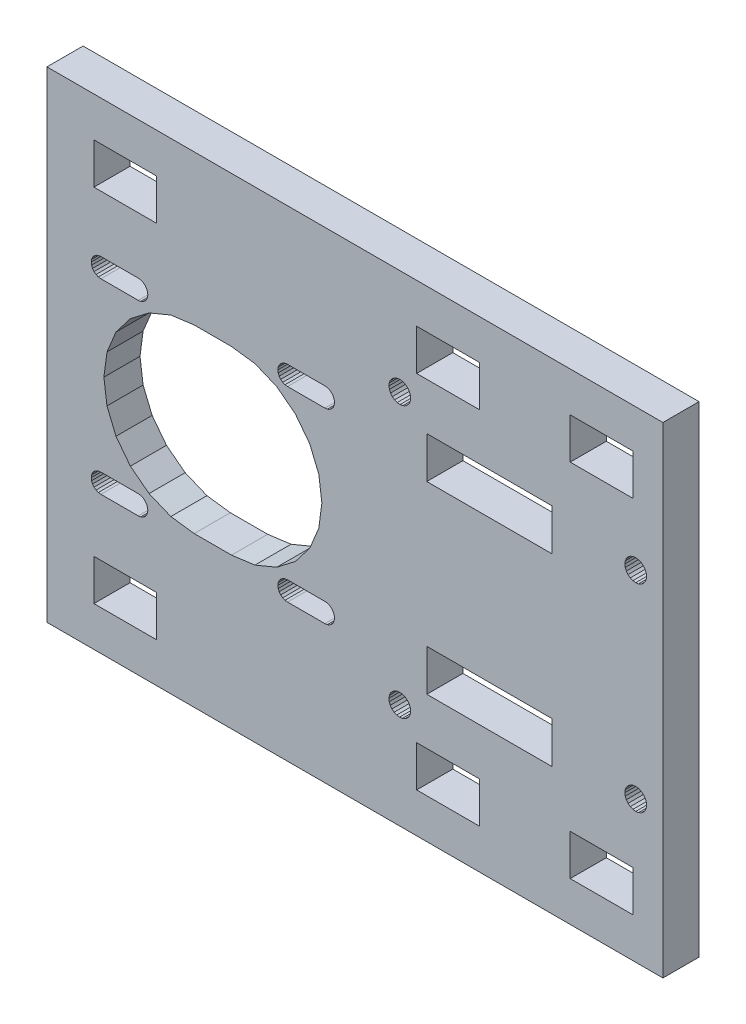
SolidWorks part; units mm, degrees
material "Maple"
ref_plane "Front Plane" through (0, 0, 0) normal (0, 0, 1) x (1, 0, 0)
ref_plane "Top Plane" through (0, 0, 0) normal (0, 1, 0) x (1, 0, 0)
ref_plane "Right Plane" through (0, 0, 0) normal (1, 0, 0) x (0, 0, -1)
sketch "Sketch1" plane through (0, 0, 0) normal (0, 0, 1) x (1, 0, 0)
  line L1749 (-500.5127, -309.2377) -> (-500.767, -309.5691)
  line L1750 (-500.767, -309.5691) -> (-500.9268, -309.955)
  line L1751 (-500.9268, -309.955) -> (-500.9814, -310.3691)
  line L1752 (-500.9814, -310.3691) -> (-500.9268, -310.7832)
  line L1753 (-500.9268, -310.7832) -> (-500.767, -311.1691)
  line L1754 (-491.6359, -309.955) -> (-491.7957, -309.5691)
  line L1755 (-491.7957, -309.5691) -> (-492.05, -309.2377)
  line L1756 (-492.05, -309.2377) -> (-492.3814, -308.9835)
  line L1757 (-492.3814, -308.9835) -> (-492.7672, -308.8236)
  line L1758 (-500.5376, -292.5691) -> (-500.5376, -299.3691)
  line L1759 (-500.5376, -299.3691) -> (-490.1376, -299.3691)
  line L1760 (-490.1376, -359.2691) -> (-490.1376, -352.4691)
  line L1761 (-490.1376, -352.4691) -> (-500.5376, -352.4691)
  line L1762 (-500.5376, -352.4691) -> (-500.5376, -359.2691)
  line L1763 (-491.6359, -310.7832) -> (-491.5814, -310.3691)
  line L1764 (-491.5814, -310.3691) -> (-491.6359, -309.955)
  line L1765 (-411.4551, -307.9103) -> (-411.021, -307.7304)
  line L1766 (-411.8279, -308.1963) -> (-411.4551, -307.9103)
  line L1767 (-406.0393, -285.9691) -> (-508.3376, -285.9691)
  line L1768 (-508.3376, -365.8691) -> (-406.0393, -365.8691)
  line L1769 (-446.9376, -299.3691) -> (-436.5376, -299.3691)
  line L1770 (-436.5376, -299.3691) -> (-436.5376, -292.5691)
  line L1771 (-421.4376, -359.2691) -> (-421.4376, -352.4691)
  line L1772 (-448.1592, -347.5539) -> (-447.9891, -347.9919)
  line L1773 (-448.4369, -347.1748) -> (-448.1592, -347.5539)
  line L1774 (-448.8033, -346.8806) -> (-448.4369, -347.1748)
  line L1775 (-469.5127, -340.2377) -> (-469.767, -340.5691)
  line L1776 (-473.7991, -311.3802) -> (-477.6814, -310.8691)
  line L1777 (-483.8814, -310.8691) -> (-477.6814, -310.8691)
  line L1778 (-483.8814, -310.8691) -> (-487.7636, -311.3802)
  line L1779 (-487.7636, -311.3802) -> (-491.3814, -312.8787)
  line L1780 (-448.8033, -304.9576) -> (-449.2333, -305.147)
  line L1781 (-448.4369, -304.6634) -> (-448.8033, -304.9576)
  line L1782 (-448.1592, -304.2843) -> (-448.4369, -304.6634)
  line L1783 (-462.6814, -325.8691) -> (-463.1925, -321.9868)
  line L1784 (-463.1925, -321.9868) -> (-464.691, -318.3691)
  line L1785 (-464.691, -318.3691) -> (-467.0747, -315.2625)
  line L1786 (-467.0747, -315.2625) -> (-470.1814, -312.8787)
  line L1787 (-492.7672, -311.9146) -> (-492.3814, -311.7547)
  line L1788 (-492.3814, -311.7547) -> (-492.05, -311.5005)
  line L1789 (-492.05, -311.5005) -> (-491.7957, -311.1691)
  line L1790 (-490.1376, -299.3691) -> (-490.1376, -292.5691)
  line L1791 (-490.1376, -292.5691) -> (-500.5376, -292.5691)
  line L1792 (-491.5814, -341.3691) -> (-491.6359, -340.955)
  line L1793 (-491.6359, -340.955) -> (-491.7957, -340.5691)
  line L1794 (-491.7957, -340.5691) -> (-492.05, -340.2377)
  line L1795 (-492.05, -340.2377) -> (-492.3814, -339.9835)
  line L1796 (-461.05, -340.2377) -> (-461.3814, -339.9835)
  line L1797 (-461.3814, -339.9835) -> (-461.7672, -339.8236)
  line L1798 (-406.0393, -365.8691) -> (-406.0393, -285.9691)
  line L1799 (-412.2937, -341.9032) -> (-412.1139, -341.4691)
  line L1800 (-449.3104, -350.1677) -> (-449.7775, -350.2187)
  line L1801 (-448.8724, -349.9975) -> (-449.3104, -350.1677)
  line L1802 (-448.4933, -349.7198) -> (-448.8724, -349.9975)
  line L1803 (-448.1991, -349.3534) -> (-448.4933, -349.7198)
  line L1804 (-498.8814, -325.8691) -> (-498.3702, -329.7514)
  line L1805 (-498.3702, -329.7514) -> (-496.8717, -333.3691)
  line L1806 (-496.8717, -333.3691) -> (-494.488, -336.4757)
  line L1807 (-494.488, -336.4757) -> (-491.3814, -338.8595)
  line L1808 (-409.2823, -310.7419) -> (-409.6551, -311.0279)
  line L1809 (-447.9891, -303.8463) -> (-448.1592, -304.2843)
  line L1810 (-450.6719, -349.9576) -> (-451.0383, -349.6634)
  line L1811 (-450.2419, -350.147) -> (-450.6719, -349.9576)
  line L1812 (-449.7775, -350.2187) -> (-450.2419, -350.147)
  line L1813 (-408.7551, -309.4691) -> (-408.8164, -309.935)
  line L1814 (-408.8164, -309.0032) -> (-408.7551, -309.4691)
  line L1815 (-408.9962, -308.5691) -> (-408.8164, -309.0032)
  line L1816 (-508.3376, -285.9691) -> (-508.3376, -365.8691)
  line L1817 (-411.4551, -340.8103) -> (-411.021, -340.6304)
  line L1818 (-448.0097, -348.9234) -> (-448.1991, -349.3534)
  line L1819 (-421.4376, -359.2691) -> (-411.0376, -359.2691)
  line L1820 (-411.0376, -359.2691) -> (-411.0376, -352.4691)
  line L1821 (-411.0376, -352.4691) -> (-421.4376, -352.4691)
  line L1822 (-469.1814, -311.7547) -> (-468.7955, -311.9146)
  line L1823 (-468.7955, -311.9146) -> (-468.3814, -311.9691)
  line L1824 (-468.3814, -311.9691) -> (-462.1814, -311.9691)
  line L1825 (-462.1814, -311.9691) -> (-461.7672, -311.9146)
  line L1826 (-461.7672, -311.9146) -> (-461.3814, -311.7547)
  line L1827 (-424.4866, -344.6691) -> (-445.2551, -344.6691)
  line L1828 (-424.4866, -344.6691) -> (-424.4866, -337.7691)
  line L1829 (-424.4866, -337.7691) -> (-445.2551, -337.7691)
  line L1830 (-469.1814, -342.7547) -> (-468.7955, -342.9146)
  line L1831 (-468.7955, -342.9146) -> (-468.3814, -342.9691)
  line L1832 (-468.3814, -342.9691) -> (-462.1814, -342.9691)
  line L1833 (-469.9268, -340.955) -> (-469.9814, -341.3691)
  line L1834 (-469.9814, -341.3691) -> (-469.9268, -341.7832)
  line L1835 (-469.9268, -341.7832) -> (-469.767, -342.1691)
  line L1836 (-469.767, -342.1691) -> (-469.5127, -342.5005)
  line L1837 (-500.1814, -339.9835) -> (-500.5127, -340.2377)
  line L1838 (-500.5127, -340.2377) -> (-500.767, -340.5691)
  line L1839 (-500.767, -340.5691) -> (-500.9268, -340.955)
  line L1840 (-500.9268, -340.955) -> (-500.9814, -341.3691)
  line L1841 (-445.2551, -337.7691) -> (-445.2551, -344.6691)
  line L1842 (-424.4866, -314.0691) -> (-445.2551, -314.0691)
  line L1843 (-424.4866, -314.0691) -> (-424.4866, -307.1691)
  line L1844 (-462.1814, -342.9691) -> (-461.7672, -342.9146)
  line L1845 (-461.7672, -342.9146) -> (-461.3814, -342.7547)
  line L1846 (-461.3814, -342.7547) -> (-461.05, -342.5005)
  line L1847 (-461.05, -342.5005) -> (-460.7957, -342.1691)
  line L1848 (-460.7957, -342.1691) -> (-460.6359, -341.7832)
  line L1849 (-412.1139, -341.4691) -> (-411.8279, -341.0963)
  line L1850 (-412.3551, -342.3691) -> (-412.2937, -341.9032)
  line L1851 (-412.2937, -342.835) -> (-412.3551, -342.3691)
  line L1852 (-408.9962, -341.4691) -> (-408.8164, -341.9032)
  line L1853 (-409.2823, -341.0963) -> (-408.9962, -341.4691)
  line L1854 (-409.6551, -340.8103) -> (-409.2823, -341.0963)
  line L1855 (-451.2761, -304.3534) -> (-451.4655, -303.9234)
  line L1856 (-450.9819, -304.7198) -> (-451.2761, -304.3534)
  line L1857 (-450.6029, -304.9975) -> (-450.9819, -304.7198)
  line L1858 (-450.6719, -301.8806) -> (-450.2419, -301.6912)
  line L1859 (-451.0383, -302.1748) -> (-450.6719, -301.8806)
  line L1860 (-451.316, -302.5539) -> (-451.0383, -302.1748)
  line L1861 (-448.4933, -302.1184) -> (-448.1991, -302.4848)
  line L1862 (-448.8724, -301.8407) -> (-448.4933, -302.1184)
  line L1863 (-421.4376, -299.3691) -> (-421.4376, -292.5691)
  line L1864 (-421.4376, -299.3691) -> (-411.0376, -299.3691)
  line L1865 (-412.1139, -343.2691) -> (-412.2937, -342.835)
  line L1866 (-411.8279, -343.6419) -> (-412.1139, -343.2691)
  line L1867 (-411.4551, -343.9279) -> (-411.8279, -343.6419)
  line L1868 (-461.7672, -339.8236) -> (-462.1814, -339.7691)
  line L1869 (-411.021, -311.2078) -> (-411.4551, -311.0279)
  line L1870 (-410.5551, -311.2691) -> (-411.021, -311.2078)
  line L1871 (-409.6551, -311.0279) -> (-410.0892, -311.2078)
  line L1872 (-449.2333, -346.6912) -> (-448.8033, -346.8806)
  line L1873 (-449.6977, -346.6195) -> (-449.2333, -346.6912)
  line L1874 (-450.1649, -346.6705) -> (-449.6977, -346.6195)
  line L1875 (-409.2823, -308.1963) -> (-408.9962, -308.5691)
  line L1876 (-409.6551, -307.9103) -> (-409.2823, -308.1963)
  line L1877 (-461.7672, -308.8236) -> (-462.1814, -308.7691)
  line L1878 (-468.3814, -308.7691) -> (-462.1814, -308.7691)
  line L1879 (-468.3814, -308.7691) -> (-468.7955, -308.8236)
  line L1880 (-468.7955, -308.8236) -> (-469.1814, -308.9835)
  line L1881 (-469.1814, -308.9835) -> (-469.5127, -309.2377)
  line L1882 (-469.5127, -309.2377) -> (-469.767, -309.5691)
  line L1883 (-469.767, -309.5691) -> (-469.9268, -309.955)
  line L1884 (-469.9268, -309.955) -> (-469.9814, -310.3691)
  line L1885 (-469.9814, -310.3691) -> (-469.9268, -310.7832)
  line L1886 (-408.9962, -310.3691) -> (-409.2823, -310.7419)
  line L1887 (-408.8164, -309.935) -> (-408.9962, -310.3691)
  line L1888 (-492.7672, -308.8236) -> (-493.1814, -308.7691)
  line L1889 (-499.3814, -308.7691) -> (-493.1814, -308.7691)
  line L1890 (-499.3814, -308.7691) -> (-499.7955, -308.8236)
  line L1891 (-499.7955, -308.8236) -> (-500.1814, -308.9835)
  line L1892 (-500.1814, -308.9835) -> (-500.5127, -309.2377)
  line L1893 (-411.021, -344.1078) -> (-411.4551, -343.9279)
  line L1894 (-410.5551, -344.1691) -> (-411.021, -344.1078)
  line L1895 (-409.6551, -343.9279) -> (-410.0892, -344.1078)
  line L1896 (-409.2823, -343.6419) -> (-409.6551, -343.9279)
  line L1897 (-469.9268, -310.7832) -> (-469.767, -311.1691)
  line L1898 (-469.767, -311.1691) -> (-469.5127, -311.5005)
  line L1899 (-469.5127, -311.5005) -> (-469.1814, -311.7547)
  line L1900 (-451.4862, -302.9919) -> (-451.316, -302.5539)
  line L1901 (-451.5372, -303.459) -> (-451.4862, -302.9919)
  line L1902 (-451.4655, -303.9234) -> (-451.5372, -303.459)
  line L1903 (-500.9814, -341.3691) -> (-500.9268, -341.7832)
  line L1904 (-500.9268, -341.7832) -> (-500.767, -342.1691)
  line L1905 (-500.767, -342.1691) -> (-500.5127, -342.5005)
  line L1906 (-500.5127, -342.5005) -> (-500.1814, -342.7547)
  line L1907 (-424.4866, -307.1691) -> (-445.2551, -307.1691)
  line L1908 (-445.2551, -307.1691) -> (-445.2551, -314.0691)
  line L1909 (-436.5376, -352.4691) -> (-446.9376, -352.4691)
  line L1910 (-446.9376, -352.4691) -> (-446.9376, -359.2691)
  line L1911 (-412.1139, -308.5691) -> (-411.8279, -308.1963)
  line L1912 (-412.2937, -309.0032) -> (-412.1139, -308.5691)
  line L1913 (-436.5376, -359.2691) -> (-436.5376, -352.4691)
  line L1914 (-436.5376, -292.5691) -> (-446.9376, -292.5691)
  line L1915 (-446.9376, -292.5691) -> (-446.9376, -299.3691)
  line L1916 (-410.0892, -307.7304) -> (-409.6551, -307.9103)
  line L1917 (-410.5551, -307.6691) -> (-410.0892, -307.7304)
  line L1918 (-411.021, -307.7304) -> (-410.5551, -307.6691)
  line L1919 (-450.6029, -346.8407) -> (-450.1649, -346.6705)
  line L1920 (-450.9819, -347.1184) -> (-450.6029, -346.8407)
  line L1921 (-451.2761, -347.4848) -> (-450.9819, -347.1184)
  line L1922 (-451.4655, -347.9148) -> (-451.2761, -347.4848)
  line L1923 (-447.9891, -347.9919) -> (-447.9381, -348.459)
  line L1924 (-410.0892, -311.2078) -> (-410.5551, -311.2691)
  line L1925 (-446.9376, -359.2691) -> (-436.5376, -359.2691)
  line L1926 (-450.1649, -305.1677) -> (-450.6029, -304.9975)
  line L1927 (-449.6977, -305.2187) -> (-450.1649, -305.1677)
  line L1928 (-449.2333, -305.147) -> (-449.6977, -305.2187)
  line L1929 (-461.3814, -311.7547) -> (-461.05, -311.5005)
  line L1930 (-461.05, -311.5005) -> (-460.7957, -311.1691)
  line L1931 (-460.7957, -311.1691) -> (-460.6359, -310.7832)
  line L1932 (-460.6359, -310.7832) -> (-460.5814, -310.3691)
  line L1933 (-460.5814, -310.3691) -> (-460.6359, -309.955)
  line L1934 (-491.7957, -311.1691) -> (-491.6359, -310.7832)
  line L1935 (-499.7955, -339.8236) -> (-500.1814, -339.9835)
  line L1936 (-469.5127, -342.5005) -> (-469.1814, -342.7547)
  line L1937 (-468.3814, -339.7691) -> (-462.1814, -339.7691)
  line L1938 (-468.3814, -339.7691) -> (-468.7955, -339.8236)
  line L1939 (-468.7955, -339.8236) -> (-469.1814, -339.9835)
  line L1940 (-469.1814, -339.9835) -> (-469.5127, -340.2377)
  line L1941 (-410.5551, -340.5691) -> (-410.0892, -340.6304)
  line L1942 (-411.021, -340.6304) -> (-410.5551, -340.5691)
  line L1943 (-411.8279, -341.0963) -> (-411.4551, -340.8103)
  line L1944 (-447.9381, -348.459) -> (-448.0097, -348.9234)
  line L1945 (-491.7957, -342.1691) -> (-491.6359, -341.7832)
  line L1946 (-491.6359, -341.7832) -> (-491.5814, -341.3691)
  line L1947 (-412.3551, -309.4691) -> (-412.2937, -309.0032)
  line L1948 (-447.9381, -303.3792) -> (-447.9891, -303.8463)
  line L1949 (-448.0097, -302.9148) -> (-447.9381, -303.3792)
  line L1950 (-448.1991, -302.4848) -> (-448.0097, -302.9148)
  line L1951 (-492.7672, -342.9146) -> (-492.3814, -342.7547)
  line L1952 (-492.3814, -342.7547) -> (-492.05, -342.5005)
  line L1953 (-492.05, -342.5005) -> (-491.7957, -342.1691)
  line L1954 (-469.767, -340.5691) -> (-469.9268, -340.955)
  line L1955 (-470.1814, -312.8787) -> (-473.7991, -311.3802)
  line L1956 (-460.6359, -309.955) -> (-460.7957, -309.5691)
  line L1957 (-460.7957, -309.5691) -> (-461.05, -309.2377)
  line L1958 (-461.05, -309.2377) -> (-461.3814, -308.9835)
  line L1959 (-461.3814, -308.9835) -> (-461.7672, -308.8236)
  line L1960 (-470.1814, -338.8595) -> (-467.0747, -336.4757)
  line L1961 (-467.0747, -336.4757) -> (-464.691, -333.3691)
  line L1962 (-464.691, -333.3691) -> (-463.1925, -329.7514)
  line L1963 (-463.1925, -329.7514) -> (-462.6814, -325.8691)
  line L1964 (-500.1814, -342.7547) -> (-499.7955, -342.9146)
  line L1965 (-499.7955, -342.9146) -> (-499.3814, -342.9691)
  line L1966 (-499.3814, -342.9691) -> (-493.1814, -342.9691)
  line L1967 (-493.1814, -342.9691) -> (-492.7672, -342.9146)
  line L1968 (-500.767, -311.1691) -> (-500.5127, -311.5005)
  line L1969 (-500.5127, -311.5005) -> (-500.1814, -311.7547)
  line L1970 (-500.1814, -311.7547) -> (-499.7955, -311.9146)
  line L1971 (-499.7955, -311.9146) -> (-499.3814, -311.9691)
  line L1972 (-499.3814, -311.9691) -> (-493.1814, -311.9691)
  line L1973 (-493.1814, -311.9691) -> (-492.7672, -311.9146)
  line L1974 (-451.5372, -348.3792) -> (-451.4655, -347.9148)
  line L1975 (-451.4862, -348.8463) -> (-451.5372, -348.3792)
  line L1976 (-451.316, -349.2843) -> (-451.4862, -348.8463)
  line L1977 (-451.0383, -349.6634) -> (-451.316, -349.2843)
  line L1978 (-412.1139, -310.3691) -> (-412.2937, -309.935)
  line L1979 (-411.8279, -310.7419) -> (-412.1139, -310.3691)
  line L1980 (-411.4551, -311.0279) -> (-411.8279, -310.7419)
  line L1981 (-410.0892, -340.6304) -> (-409.6551, -340.8103)
  line L1982 (-410.0892, -344.1078) -> (-410.5551, -344.1691)
  line L1983 (-408.9962, -343.2691) -> (-409.2823, -343.6419)
  line L1984 (-412.2937, -309.935) -> (-412.3551, -309.4691)
  line L1985 (-500.5376, -359.2691) -> (-490.1376, -359.2691)
  line L1986 (-460.6359, -341.7832) -> (-460.5814, -341.3691)
  line L1987 (-460.5814, -341.3691) -> (-460.6359, -340.955)
  line L1988 (-460.6359, -340.955) -> (-460.7957, -340.5691)
  line L1989 (-460.7957, -340.5691) -> (-461.05, -340.2377)
  line L1990 (-449.3104, -301.6705) -> (-448.8724, -301.8407)
  line L1991 (-449.7775, -301.6195) -> (-449.3104, -301.6705)
  line L1992 (-450.2419, -301.6912) -> (-449.7775, -301.6195)
  line L1993 (-408.8164, -342.835) -> (-408.9962, -343.2691)
  line L1994 (-408.7551, -342.3691) -> (-408.8164, -342.835)
  line L1995 (-408.8164, -341.9032) -> (-408.7551, -342.3691)
  line L1996 (-492.3814, -339.9835) -> (-492.7672, -339.8236)
  line L1997 (-492.7672, -339.8236) -> (-493.1814, -339.7691)
  line L1998 (-499.3814, -339.7691) -> (-493.1814, -339.7691)
  line L1999 (-499.3814, -339.7691) -> (-499.7955, -339.8236)
  line L2000 (-491.3814, -312.8787) -> (-494.488, -315.2625)
  line L2001 (-494.488, -315.2625) -> (-496.8717, -318.3691)
  line L2002 (-496.8717, -318.3691) -> (-498.3702, -321.9868)
  line L2003 (-498.3702, -321.9868) -> (-498.8814, -325.8691)
  line L2004 (-491.3814, -338.8595) -> (-487.7636, -340.358)
  line L2005 (-487.7636, -340.358) -> (-483.8814, -340.8691)
  line L2006 (-483.8814, -340.8691) -> (-477.6814, -340.8691)
  line L2007 (-477.6814, -340.8691) -> (-473.7991, -340.358)
  line L2008 (-473.7991, -340.358) -> (-470.1814, -338.8595)
  line L2009 (-411.0376, -292.5691) -> (-421.4376, -292.5691)
  line L2010 (-411.0376, -299.3691) -> (-411.0376, -292.5691)
  line L8881 (-435.0308, -327.9523) -> (-435.0308, -325.9294)
  line L8882 (-435.0308, -325.9294) -> (-436.1109, -323.6444)
  line L8883 (-436.1109, -323.6444) -> (-435.0308, -325.9294)
  line L8884 (-435.0308, -325.9294) -> (-433.9693, -323.6444)
  line L8885 (-433.9693, -323.6444) -> (-435.0308, -325.9294)
  line L8886 (-435.0308, -325.9294) -> (-435.0308, -327.9523)
extrude "Boss-Extrude1" add sketch "Sketch1" along normal blind 6
